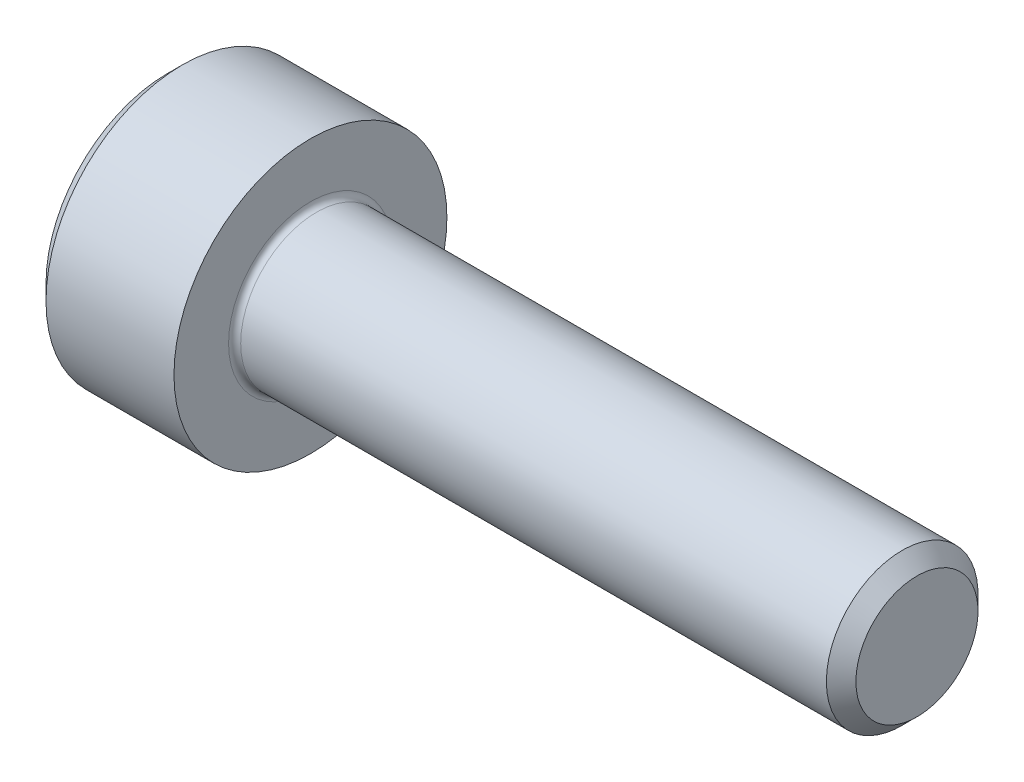
SolidWorks part; units mm, degrees
ref_plane "Front Plane" through (0, 0, 0) normal (0, 0, 1) x (1, 0, 0)
ref_plane "Top Plane" through (0, 0, 0) normal (0, 1, 0) x (1, 0, 0)
ref_plane "Right Plane" through (0, 0, 0) normal (1, 0, 0) x (0, 0, -1)
ref_plane "Plane1" through (0, 0, 0) normal (0, 0, 1) x (1, 0, 0)
sketch "Sketch1" plane through (0, 0, 0) normal (0, 0, 1) x (1, 0, 0)
  line L0 (-2.36, 0) -> (-2.36, 2)
  line L1 (-2.36, 2) -> (-2.11, 2.25)
  line L2 (-2.11, 2.25) -> (0, 2.25)
  line L3 (0, 2.25) -> (0, 1.35)
  line L4 (0.1, 1.25) -> (9.7565, 1.25)
  line L5 (9.7565, 1.25) -> (10, 1.0065)
  line L6 (10, 1.0065) -> (10, 0)
  line L7 (10, 0) -> (-2.36, 0)
  line L8 (10, 0) -> (-2.36, 0) construction
  arc A0 (0, 1.35) -> (0.1, 1.25) centre (0.1, 1.35) ccw
revolve "Revolve1" add sketch "Sketch1" angle 360 about L8
ref_plane "Plane2" through (-2.36, 0, 0) normal (1, 0, 0) x (0, 0, -1)
sketch "Sketch2" plane through (-2.36, 0, 0) normal (1, 0, 0) x (0, 0, -1)
  line L0 (-1, 0.5774) -> (-1, -0.5774)
  line L1 (-1, -0.5774) -> (0, -1.1547)
  line L2 (0, -1.1547) -> (1, -0.5774)
  line L3 (1, -0.5774) -> (1, 0.5774)
  line L4 (1, 0.5774) -> (0, 1.1547)
  line L5 (0, 1.1547) -> (-1, 0.5774)
extrude "Cut-Extrude1" cut sketch "Sketch2" along normal blind 1.1
ref_plane "Plane3" through (0, 0, 0) normal (0, 0, 1) x (1, 0, 0)
sketch "Sketch3" plane through (0, 0, 0) normal (0, 0, 1) x (1, 0, 0)
  line L0 (-1.26, 0) -> (-1.26, 1)
  line L1 (-1.26, 1) -> (-0.6826, 0)
  line L2 (-0.6826, 0) -> (-1.26, 0)
  line L3 (-0.6826, 0) -> (-1.26, 0) construction
revolve "Cut-Revolve1" cut sketch "Sketch3" angle 360 about L3
